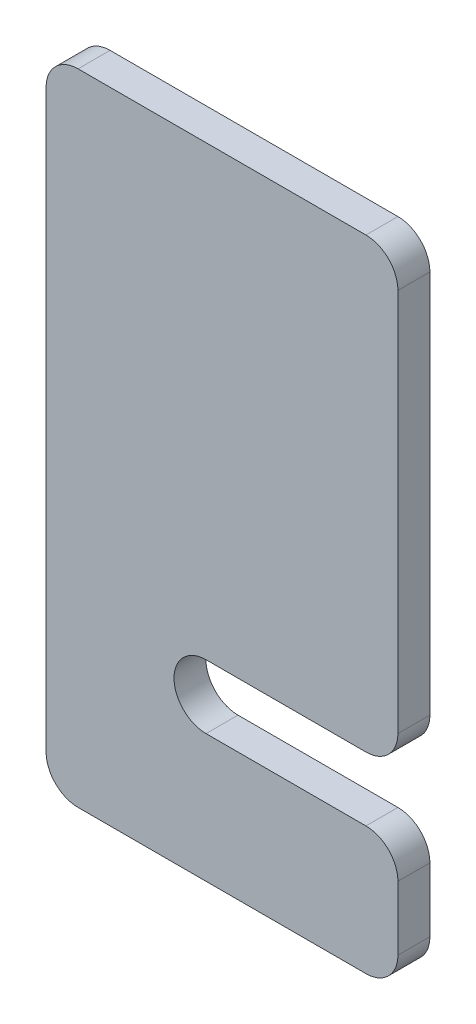
SolidWorks part; units mm, degrees
ref_plane "Plan de face" through (0, 0, 0) normal (0, 0, 1) x (1, 0, 0)
ref_plane "Plan de dessus" through (0, 0, 0) normal (0, 1, 0) x (1, 0, 0)
ref_plane "Plan de droite" through (0, 0, 0) normal (1, 0, 0) x (0, 0, -1)
sketch "Esquisse1" plane through (0, 0, 0) normal (0, 0, 1) x (1, 0, 0)
  line L0 (55, 95) -> (55, 35)
  line L1 (5, 0) -> (50, 0)
  line L2 (0, 5) -> (0, 95)
  line L3 (5, 100) -> (50, 100)
  line L4 (55, 0) -> (55, 100) construction
  line L5 (50, 30) -> (25, 30)
  line L7 (25, 20) -> (50, 20)
  line L9 (55, 15) -> (55, 5)
  arc A0 (5, 0) -> (0, 5) centre (5, 5) cw
  arc A1 (25, 30) -> (25, 20) centre (25, 25) ccw
  arc A2 (50, 20) -> (55, 15) centre (50, 15) cw
  arc A3 (50, 30) -> (55, 35) centre (50, 35) ccw
  arc A4 (55, 5) -> (50, 0) centre (50, 5) cw
  arc A6 (50, 100) -> (55, 95) centre (50, 95) cw
  arc A7 (0, 95) -> (5, 100) centre (5, 95) cw
  point P11 (0, 0)
  point P14 (55, 20)
  point P18 (55, 30)
  point P23 (55, 20)
  point P26 (55, 30)
  point P32 (0, 100)
  dimension "D6" = 5
  dimension "D5" = 25
  dimension "D4" = 5
  dimension "D7" = 5
  dimension "D8" = 5
  dimension "D1" = 100
  dimension "D2" = 55
  dimension "D3" = 20
extrude "Boss.-Extru.1" add sketch "Esquisse1" along normal blind 5
